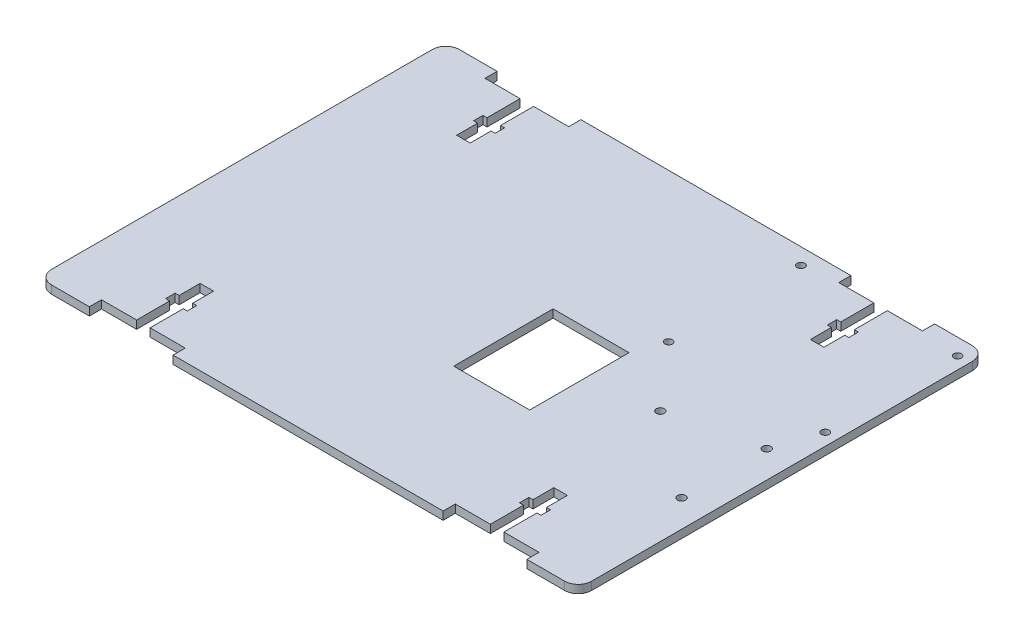
SolidWorks part; units mm, degrees
ref_plane "Front Plane" through (0, 0, 0) normal (0, 0, 1) x (1, 0, 0)
ref_plane "Top Plane" through (0, 0, 0) normal (0, 1, 0) x (1, 0, 0)
ref_plane "Right Plane" through (0, 0, 0) normal (1, 0, 0) x (0, 0, -1)
sketch "Sketch1" plane through (0, 0, 0) normal (0, 1, 0) x (1, 0, 0)
  line L1 (-100, -75.5) -> (100, -75.5)
  line L2 (-100, -75.5) -> (-100, 75.5)
  line L3 (-100, 75.5) -> (100, 75.5)
  line L4 (100, -75.5) -> (100, 75.5)
  line L5 (-100, -75.5) -> (100, 75.5) construction
  line L6 (-100, 75.5) -> (100, -75.5) construction
  point P0 (0, 0)
extrude "Boss-Extrude1" add sketch "Sketch1" along normal blind 3
ref_plane "Plane1" through (0, 3, 0) normal (0, 1, 0) x (1, 0, 0)
sketch "Sketch2" plane through (0, 3, 0) normal (0, 1, 0) x (1, 0, 0)
  line L0 (100, 75.5) -> (-100, 75.5) construction
  line L1 (-100, 75.5) -> (-68, 75.5) construction
  line L2 (-100, 75.5) -> (-100, 47.5) construction
  line L3 (-100, 47.5) -> (-68, 47.5) construction
  line L4 (-68, 75.5) -> (-68, 47.5) construction
  line L5 (-100, 75.5) -> (-100, -75.5) construction
  line L6 (-65.5, 47.5) -> (-65.5, 57) construction
  line L7 (-68, 75.5) -> (-63, 75.5) construction
  line L8 (-68, 75.5) -> (-68, 47.5) construction
  line L9 (-68, 47.5) -> (-63, 47.5) construction
  line L10 (-63, 75.5) -> (-63, 47.5) construction
  line L11 (-68, 75.5) -> (-63, 75.5)
  line L12 (-69.5, 55.25) -> (-61.5, 55.25) construction
  line L13 (-69.5, 55.25) -> (-69.5, 58.75) construction
  line L14 (-69.5, 58.75) -> (-61.5, 58.75) construction
  line L15 (-61.5, 55.25) -> (-61.5, 58.75) construction
  line L16 (-69.5, 55.25) -> (-61.5, 58.75) construction
  line L17 (-69.5, 58.75) -> (-61.5, 55.25) construction
  line L18 (-81, 71) -> (-68, 71)
  line L19 (-63, 58.75) -> (-61.5, 58.75)
  line L20 (-61.5, 58.75) -> (-61.5, 55.25)
  line L21 (-61.5, 55.25) -> (-63, 55.25)
  line L22 (-63, 55.25) -> (-63, 47.5)
  line L23 (-63, 47.5) -> (-68, 47.5)
  line L24 (-68, 47.5) -> (-68, 55.25)
  line L25 (-68, 55.25) -> (-69.5, 55.25)
  line L26 (-69.5, 55.25) -> (-69.5, 58.75)
  line L27 (-69.5, 58.75) -> (-68, 58.75)
  line L28 (-68, 71) -> (-68, 58.75)
  line L29 (-65.5, 75.5) -> (-50, 75.5) construction
  line L30 (-81, 75.5) -> (-50, 75.5) construction
  line L31 (-50, 71) -> (-63, 71)
  line L32 (-81, 75.5) -> (-50, 75.5)
  line L33 (-81, 75.5) -> (-81, 71)
  line L34 (-81, 71) -> (-50, 71) construction
  line L35 (-50, 75.5) -> (-50, 71)
  line L36 (-63, 71) -> (-63, 58.75)
  line L37 (-63, 58.75) -> (-62.9809, 58.8083)
  line L38 (0, -75.5) -> (0, 75.5) construction
  line L39 (-100, 0) -> (100, 0) construction
  line L40 (81, 71) -> (50, 71) construction
  line L41 (81, 75.5) -> (50, 75.5) construction
  line L42 (65.5, 75.5) -> (50, 75.5) construction
  line L43 (69.5, 58.75) -> (61.5, 55.25) construction
  line L44 (69.5, 55.25) -> (61.5, 58.75) construction
  line L45 (61.5, 55.25) -> (61.5, 58.75) construction
  line L46 (69.5, 58.75) -> (61.5, 58.75) construction
  line L47 (69.5, 55.25) -> (69.5, 58.75) construction
  line L48 (69.5, 55.25) -> (61.5, 55.25) construction
  line L49 (63, 75.5) -> (63, 47.5) construction
  line L50 (68, 47.5) -> (63, 47.5) construction
  line L51 (68, 75.5) -> (68, 47.5) construction
  line L52 (68, 75.5) -> (63, 75.5) construction
  line L53 (65.5, 47.5) -> (65.5, 57) construction
  line L54 (68, 75.5) -> (68, 47.5) construction
  line L56 (100, 75.5) -> (100, 47.5) construction
  line L57 (100, 75.5) -> (68, 75.5) construction
  line L58 (63, 58.75) -> (62.9809, 58.8083)
  line L59 (63, 71) -> (63, 58.75)
  line L60 (50, 75.5) -> (50, 71)
  line L61 (81, 75.5) -> (81, 71)
  line L62 (81, 75.5) -> (50, 75.5)
  line L63 (50, 71) -> (63, 71)
  line L64 (68, 71) -> (68, 58.75)
  line L65 (69.5, 58.75) -> (68, 58.75)
  line L66 (69.5, 55.25) -> (69.5, 58.75)
  line L67 (68, 55.25) -> (69.5, 55.25)
  line L68 (68, 47.5) -> (68, 55.25)
  line L69 (63, 47.5) -> (68, 47.5)
  line L70 (63, 55.25) -> (63, 47.5)
  line L71 (61.5, 55.25) -> (63, 55.25)
  line L72 (61.5, 58.75) -> (61.5, 55.25)
  line L73 (63, 58.75) -> (61.5, 58.75)
  line L74 (81, 71) -> (68, 71)
  line L75 (68, 75.5) -> (63, 75.5)
  line L76 (100, -75.5) -> (100, 75.5) construction
  line L77 (100, -75.5) -> (68, -75.5) construction
  line L78 (100, -75.5) -> (100, -47.5) construction
  line L79 (100, -47.5) -> (68, -47.5) construction
  line L80 (68, -75.5) -> (68, -47.5) construction
  line L81 (65.5, -47.5) -> (65.5, -57) construction
  line L82 (68, -75.5) -> (63, -75.5) construction
  line L83 (68, -75.5) -> (68, -47.5) construction
  line L84 (68, -47.5) -> (63, -47.5) construction
  line L85 (63, -75.5) -> (63, -47.5) construction
  line L86 (69.5, -55.25) -> (61.5, -55.25) construction
  line L87 (69.5, -55.25) -> (69.5, -58.75) construction
  line L88 (69.5, -58.75) -> (61.5, -58.75) construction
  line L89 (61.5, -55.25) -> (61.5, -58.75) construction
  line L90 (69.5, -55.25) -> (61.5, -58.75) construction
  line L91 (69.5, -58.75) -> (61.5, -55.25) construction
  line L92 (65.5, -75.5) -> (50, -75.5) construction
  line L93 (81, -75.5) -> (50, -75.5) construction
  line L94 (81, -71) -> (50, -71) construction
  line L95 (-81, -71) -> (-50, -71) construction
  line L96 (-81, -75.5) -> (-50, -75.5) construction
  line L97 (-65.5, -75.5) -> (-50, -75.5) construction
  line L98 (-69.5, -58.75) -> (-61.5, -55.25) construction
  line L99 (-69.5, -55.25) -> (-61.5, -58.75) construction
  line L100 (-61.5, -55.25) -> (-61.5, -58.75) construction
  line L101 (-69.5, -58.75) -> (-61.5, -58.75) construction
  line L102 (-69.5, -55.25) -> (-69.5, -58.75) construction
  line L103 (-69.5, -55.25) -> (-61.5, -55.25) construction
  line L104 (-63, -75.5) -> (-63, -47.5) construction
  line L105 (-68, -47.5) -> (-63, -47.5) construction
  line L106 (-68, -75.5) -> (-68, -47.5) construction
  line L107 (-68, -75.5) -> (-63, -75.5) construction
  line L108 (-65.5, -47.5) -> (-65.5, -57) construction
  line L109 (-68, -75.5) -> (-68, -47.5) construction
  line L110 (-100, -47.5) -> (-68, -47.5) construction
  line L111 (-100, -75.5) -> (-100, -47.5) construction
  line L112 (-100, -75.5) -> (-68, -75.5) construction
  line L113 (68, -75.5) -> (63, -75.5)
  line L114 (81, -71) -> (68, -71)
  line L115 (63, -58.75) -> (61.5, -58.75)
  line L116 (61.5, -58.75) -> (61.5, -55.25)
  line L117 (61.5, -55.25) -> (63, -55.25)
  line L118 (63, -55.25) -> (63, -47.5)
  line L119 (63, -47.5) -> (68, -47.5)
  line L120 (68, -47.5) -> (68, -55.25)
  line L121 (68, -55.25) -> (69.5, -55.25)
  line L122 (69.5, -55.25) -> (69.5, -58.75)
  line L123 (69.5, -58.75) -> (68, -58.75)
  line L124 (68, -71) -> (68, -58.75)
  line L125 (50, -71) -> (63, -71)
  line L126 (81, -75.5) -> (50, -75.5)
  line L127 (81, -75.5) -> (81, -71)
  line L128 (50, -75.5) -> (50, -71)
  line L129 (63, -71) -> (63, -58.75)
  line L130 (63, -58.75) -> (62.9809, -58.8083)
  line L131 (-63, -58.75) -> (-62.9809, -58.8083)
  line L132 (-63, -71) -> (-63, -58.75)
  line L133 (-50, -75.5) -> (-50, -71)
  line L134 (-81, -75.5) -> (-81, -71)
  line L135 (-81, -75.5) -> (-50, -75.5)
  line L136 (-50, -71) -> (-63, -71)
  line L137 (-68, -71) -> (-68, -58.75)
  line L138 (-69.5, -58.75) -> (-68, -58.75)
  line L139 (-69.5, -55.25) -> (-69.5, -58.75)
  line L140 (-68, -55.25) -> (-69.5, -55.25)
  line L141 (-68, -47.5) -> (-68, -55.25)
  line L142 (-63, -47.5) -> (-68, -47.5)
  line L143 (-63, -55.25) -> (-63, -47.5)
  line L144 (-61.5, -55.25) -> (-63, -55.25)
  line L145 (-61.5, -58.75) -> (-61.5, -55.25)
  line L146 (-63, -58.75) -> (-61.5, -58.75)
  line L147 (-81, -71) -> (-68, -71)
  line L148 (-68, -75.5) -> (-63, -75.5)
  line L149 (100, 0) -> (24, 0) construction
  line L150 (24, 75.5) -> (24, 0.5) construction
  line L151 (24, -75.5) -> (24, -10.5) construction
  line L152 (-100, -75.5) -> (100, -75.5) construction
  line L153 (24, 0.5) -> (15, 0.5) construction
  line L154 (19.5, -10.5) -> (19.5, -16) construction
  line L155 (15, 0.5) -> (24, 0.5) construction
  line L156 (15, 0.5) -> (15, -10.5) construction
  line L157 (15, -10.5) -> (24, -10.5) construction
  line L158 (24, 0.5) -> (24, -10.5) construction
  line L159 (19.5, -16) -> (6.75, -16) construction
  line L160 (-100, 75.5) -> (-89.3934, 64.8934) construction
  line L161 (6.75, -16) -> (32, -16) construction
  line L162 (6.75, -16) -> (6.75, 8.5) construction
  line L163 (6.75, 8.5) -> (32, 8.5) construction
  line L164 (32, -16) -> (32, 8.5) construction
  line L165 (-89.3934, 64.8934) -> (-89.3934, -5.1066) construction
  line L166 (89.92, -27.12) -> (89.92, 4.39) construction
  line L167 (-89.3934, -5.1066) -> (-29.3934, -5.1066) construction
  line L168 (-89.3934, -5.1066) -> (-89.3934, 64.8934) construction
  line L169 (-89.3934, 64.8934) -> (-29.3934, 64.8934) construction
  line L170 (-29.3934, -5.1066) -> (-29.3934, 64.8934) construction
  line L171 (100, -75.5) -> (89.92, -75.5) construction
  line L172 (100, -75.5) -> (100, -27.12) construction
  line L173 (100, -27.12) -> (89.92, -27.12) construction
  line L174 (89.92, -75.5) -> (89.92, -27.12) construction
  line L175 (89.92, -6.4831) -> (58.16, -6.4831)
  line L176 (58.16, -75.5) -> (58.16, -3.22) construction
  line L177 (95.5, 69.5) -> (95.5, 20.5) construction
  line L178 (6.75, -16) -> (32, -16) construction
  line L179 (6.75, -16) -> (6.75, -32.0716) construction
  line L180 (6.75, -32.0716) -> (32, -32.0716) construction
  line L181 (32, -16) -> (32, -32.0716) construction
  line L182 (5.5077, 9.6842) -> (33.6375, 9.6842)
  line L183 (5.5077, 9.6842) -> (5.5077, -27.0879)
  line L184 (5.5077, -27.0879) -> (33.6375, -27.0879)
  line L185 (33.6375, 9.6842) -> (33.6375, -27.0879)
  line L186 (100, 75.5) -> (95.5, 75.5) construction
  line L187 (100, 75.5) -> (100, 65.5) construction
  line L189 (95.5, 75.5) -> (95.5, 69.5) construction
  line L191 (95.5, 20.5) -> (37.5, 20.5) construction
  line L192 (95.5, 20.5) -> (95.5, 69.5) construction
  line L193 (95.5, 69.5) -> (37.5, 69.5) construction
  line L194 (37.5, 20.5) -> (37.5, 69.5) construction
  circle A4 centre (89.92, -27.12) radius 1.5
  circle A5 centre (89.92, 4.39) radius 1.5
  circle A6 centre (58.16, -3.22) radius 1.5
  circle A7 centre (95.5, 20.5) radius 1.4
  circle A8 centre (37.5, 20.5) radius 1.4
  circle A9 centre (37.5, 69.5) radius 1.4
  circle A10 centre (95.5, 69.5) radius 1.4
  point P25 (-65.5, 75.5)
  point P78 (0, 0)
  dimension "D1" = 31.51
  dimension "D2" = 31.76
extrude "Cut-Extrude2" cut sketch "Sketch2" against normal through all
fillet "Fillet1" radius 5 4 edges at (100, 1.5, -75.5) (-100, 1.5, -75.5) (-100, 1.5, 75.5) (100, 1.5, 75.5)
